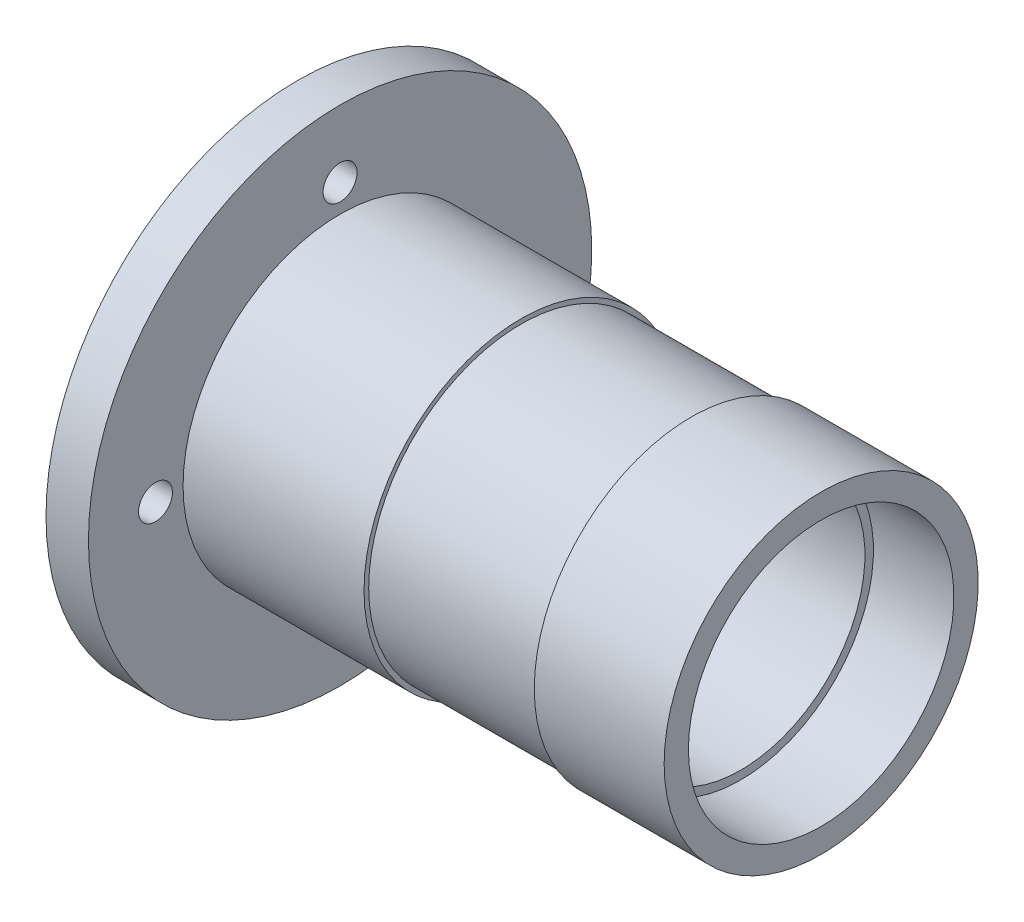
SolidWorks part; units mm, degrees
ref_plane "前视基准面" through (0, 0, 0) normal (0, 0, 1) x (1, 0, 0)
ref_plane "上视基准面" through (0, 0, 0) normal (0, 1, 0) x (1, 0, 0)
ref_plane "右视基准面" through (0, 0, 0) normal (1, 0, 0) x (0, 0, -1)
sketch "草图1" plane through (0, 0, 0) normal (0, 0, 1) x (1, 0, 0)
  line L0 (-67.0432, 0) -> (69.1067, 0) construction
  line L1 (73.2981, 37) -> (42.6981, 37)
  line L2 (42.6981, 37) -> (42.6981, 35.9)
  line L3 (42.6981, 35.9) -> (2.5781, 35.9)
  line L4 (2.5781, 35.9) -> (2.5781, 37)
  line L5 (2.5781, 37) -> (-40.0619, 37)
  line L6 (-40.0619, 37) -> (-40.0619, 59.3003)
  line L7 (-40.0619, 59.3003) -> (-50.0619, 59.3003)
  line L8 (-50.0619, 59.3003) -> (-50.0619, 31.28)
  line L9 (-50.0619, 31.28) -> (-9.0619, 31.28)
  line L10 (-9.0619, 31.28) -> (-9.0619, 29.28)
  line L11 (-9.0619, 29.28) -> (54.3381, 29.28)
  line L12 (54.3381, 29.28) -> (54.3381, 31.28)
  line L13 (54.3381, 31.28) -> (73.2981, 31.28)
  line L14 (73.2981, 31.28) -> (73.2981, 37)
  dimension "D1" = 30.6
  dimension "D2" = 37
  dimension "D3" = 31.28
  dimension "D4" = 63.4
  dimension "D5" = 2
  dimension "D6" = 2
  dimension "D7" = 35.9
  dimension "D8" = 10
  dimension "D9" = 123.36
  dimension "D10" = 41
  dimension "D11" = 11.64
  dimension "D12" = 37
revolve "旋转1" add sketch "草图1" angle 360 about L0
sketch "草图2" plane through (-50.0619, 0, 0) normal (-1, 0, 0) x (0, 0, 1)
  circle A0 centre (0, 0) radius 43.5
  circle A1 centre (0, 43.5) radius 4
  circle A2 centre (43.5, 0) radius 4
  circle A3 centre (0, -43.5) radius 4
  circle A4 centre (-43.5, 0) radius 4
  dimension "D1" = 4
extrude "切除-拉伸1" cut sketch "草图2" against normal through all contours A0 A1 | A0 A1 | A0 A3 | A0 A3 | A0 A4 | A2
